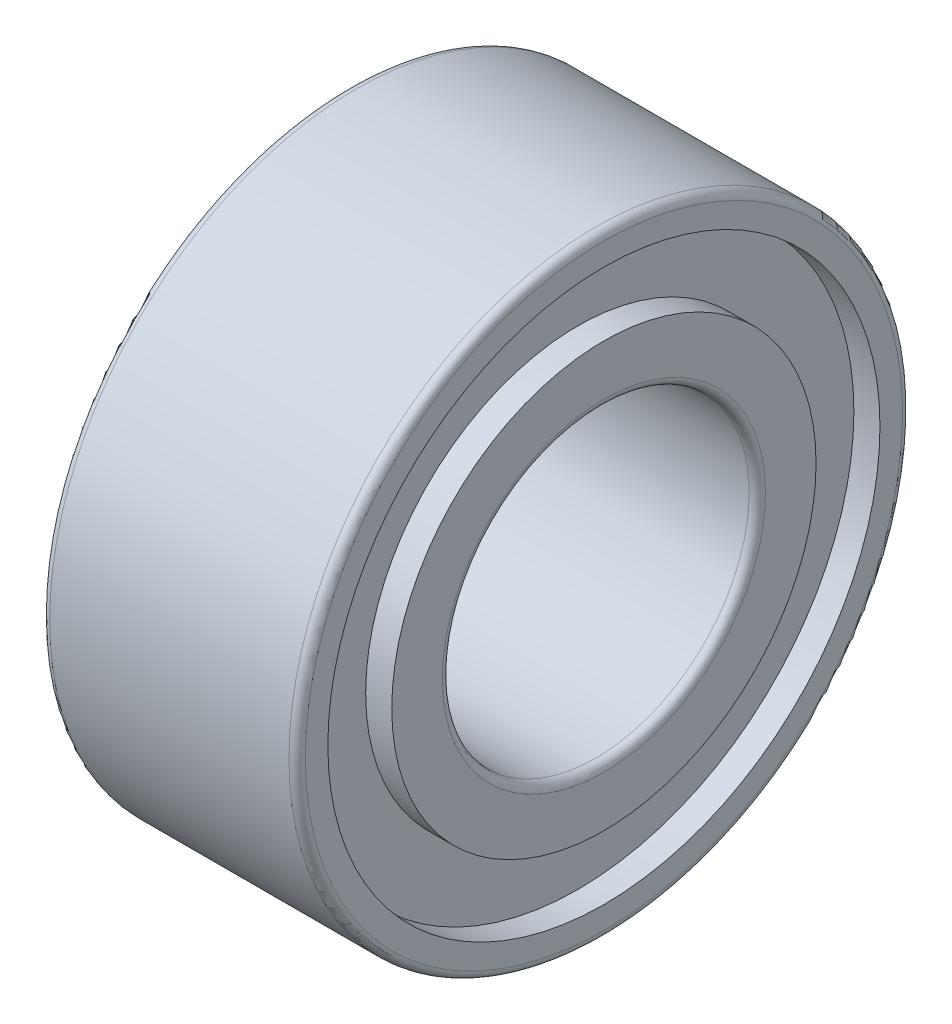
SolidWorks part; units mm, degrees
ref_plane "前视基准面" through (0, 0, 0) normal (0, 0, 1) x (1, 0, 0)
ref_plane "上视基准面" through (0, 0, 0) normal (0, 1, 0) x (1, 0, 0)
ref_plane "右视基准面" through (0, 0, 0) normal (1, 0, 0) x (0, 0, -1)
other "Configuration Table"
ref_plane "基准面1" through (0, 0, 0) normal (0, 0, -1) x (-1, 0, 0)
sketch "草图1" plane through (0, 0, 0) normal (0, 0, -1) x (-1, 0, 0)
  line L0 (0, 2.075) -> (-0.255, 2.075)
  line L1 (-0.255, 2.075) -> (-0.255, 2.7)
  line L2 (-0.255, 2.7) -> (0, 2.7)
  line L3 (0, 2.7) -> (0, 2.92)
  line L4 (-0.08, 3) -> (-2.42, 3)
  line L5 (-2.5, 2.92) -> (-2.5, 2.7)
  line L6 (-2.5, 2.7) -> (-2.245, 2.7)
  line L7 (-2.245, 2.7) -> (-2.245, 2.075)
  line L8 (-2.245, 2.075) -> (-2.5, 2.075)
  line L9 (-2.5, 2.075) -> (-2.5, 1.58)
  line L10 (-2.42, 1.5) -> (-0.08, 1.5)
  line L11 (0, 1.58) -> (0, 2.075)
  line L12 (-2.5, 0) -> (0, 0) construction
  arc A0 (0, 2.92) -> (-0.08, 3) centre (-0.08, 2.92) ccw
  arc A1 (-2.42, 3) -> (-2.5, 2.92) centre (-2.42, 2.92) ccw
  arc A2 (-2.5, 1.58) -> (-2.42, 1.5) centre (-2.42, 1.58) ccw
  arc A3 (-0.08, 1.5) -> (0, 1.58) centre (-0.08, 1.58) ccw
revolve "旋转1" add sketch "草图1" angle 360 about L12
